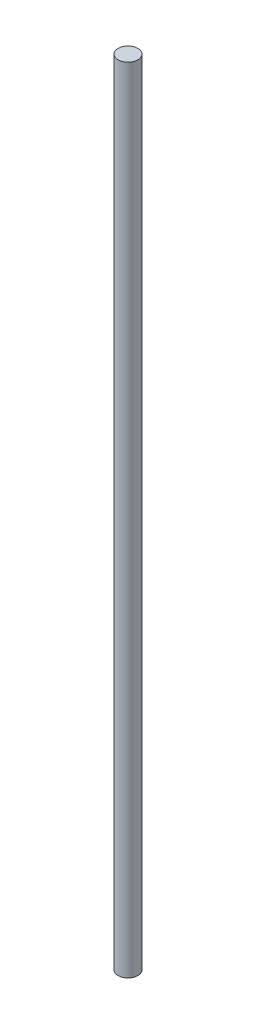
SolidWorks part; units mm, degrees
ref_plane "Front Plane" through (0, 0, 0) normal (0, 0, 1) x (1, 0, 0)
ref_plane "Top Plane" through (0, 0, 0) normal (0, 1, 0) x (1, 0, 0)
ref_plane "Right Plane" through (0, 0, 0) normal (1, 0, 0) x (0, 0, -1)
sketch "Sketch1" plane through (0, 0, 0) normal (0, 1, 0) x (1, 0, 0)
  circle A0 centre (0, 0) radius 6.35
  dimension "D1" = 12.7
extrude "Boss-Extrude1" add sketch "Sketch1" along normal blind 508
